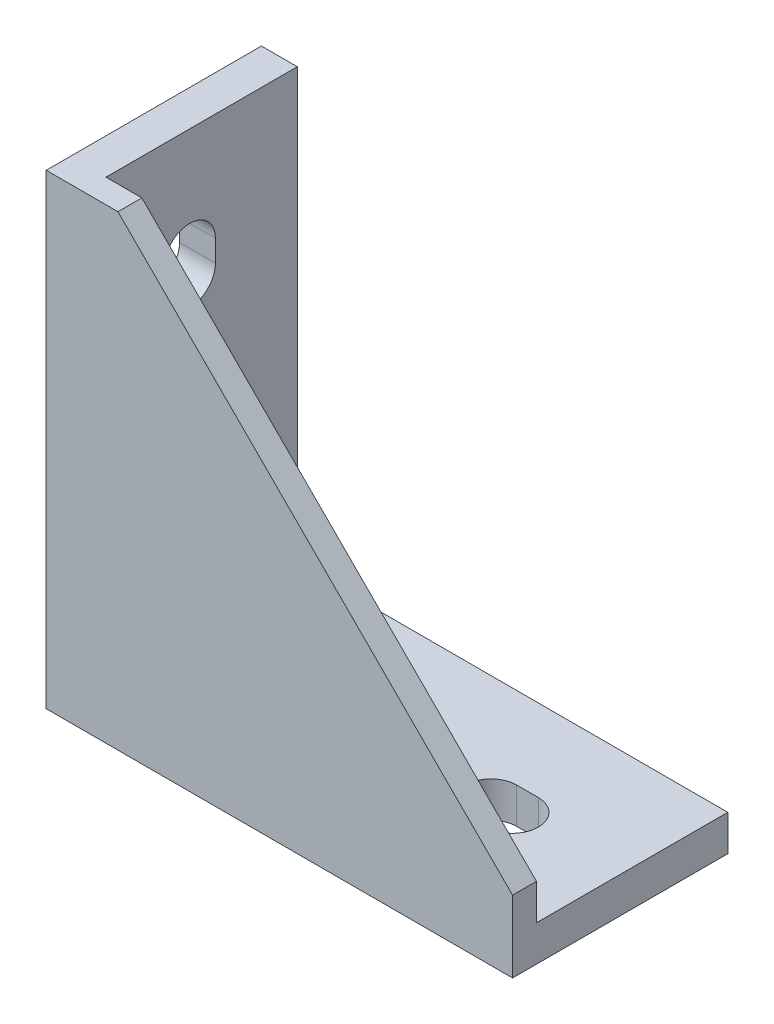
SolidWorks part; units mm, degrees
material "Алюминиевый сплав"
ref_plane "Спереди" through (0, 0, 0) normal (0, 0, 1) x (1, 0, 0)
ref_plane "Сверху" through (0, 0, 0) normal (0, 1, 0) x (1, 0, 0)
ref_plane "Справа" through (0, 0, 0) normal (1, 0, 0) x (0, 0, -1)
sketch "Эскиз1" plane through (0, 0, 0) normal (0, 0, 1) x (1, 0, 0)
  line L0 (0, 78) -> (0, 0)
  line L1 (0, 0) -> (78, 0)
  line L2 (78, 0) -> (78, 6)
  line L4 (6, 78) -> (0, 78)
  line L5 (6, 78) -> (6, 6)
  line L6 (6, 6) -> (78, 6)
  dimension "D1" = 78
  dimension "D2" = 6
extrude "Бобышка-Вытянуть1" add sketch "Эскиз1" along normal mid plane 36
sketch "Эскиз2" plane through (0, 0, 18) normal (0, 0, 1) x (1, 0, 0)
  line L1 (78, 6) -> (6, 6)
  line L2 (6, 6) -> (6, 78)
  line L3 (78, 0) -> (78, 6) construction
  line L4 (6, 78) -> (12, 78)
  line L5 (12, 78) -> (78, 12)
  line L6 (78, 12) -> (78, 6)
extrude "Бобышка-Вытянуть2" add sketch "Эскиз2" against normal blind 4
sketch "Эскиз3" plane through (0, 6, 0) normal (0, 1, 0) x (1, 0, 0)
  line L0 (18, 0) -> (31.4, 0) construction
  line L1 (18, 4.3) -> (31.4, 4.3)
  line L2 (18, -4.3) -> (31.4, -4.3)
  line L3 (0, -18) -> (0, 18) construction
  line L4 (56.4, 0) -> (60, 0) construction
  line L5 (56.4, 4.3) -> (60, 4.3)
  line L6 (56.4, -4.3) -> (60, -4.3)
  arc A0 (18, 4.3) -> (18, -4.3) centre (18, 0) ccw
  arc A1 (31.4, -4.3) -> (31.4, 4.3) centre (31.4, 0) ccw
  arc A3 (56.4, 4.3) -> (56.4, -4.3) centre (56.4, 0) ccw
  arc A4 (60, -4.3) -> (60, 4.3) centre (60, 0) ccw
  point P2 (24.7, 0)
  point P12 (58.2, 0)
  dimension "D2" = 4.3
  dimension "D3" = 18
  dimension "D4" = 3.6
  dimension "D5" = 25
  dimension "D1" = 13.4
extrude "Вырез-Вытянуть1" cut sketch "Эскиз3" against normal through all
sketch "Эскиз4" plane through (0, 0, 0) normal (0, -1, 0) x (1, 0, 0)
  line L0 (0, 18) -> (0, -18) construction
  line L1 (3, -3.75) -> (5.5, -3.75)
  line L2 (3, -3.75) -> (3, 3.75)
  line L3 (3, 3.75) -> (5.5, 3.75)
  line L4 (5.5, -3.75) -> (5.5, 3.75)
  line L5 (3, -3.75) -> (5.5, 3.75) construction
  line L6 (3, 3.75) -> (5.5, -3.75) construction
  line L7 (72.5, -3.75) -> (75, -3.75)
  line L8 (72.5, -3.75) -> (72.5, 3.75)
  line L9 (72.5, 3.75) -> (75, 3.75)
  line L10 (75, -3.75) -> (75, 3.75)
  line L11 (72.5, -3.75) -> (75, 3.75) construction
  line L12 (72.5, 3.75) -> (75, -3.75) construction
  line L13 (78, 18) -> (78, -18) construction
  point P0 (4.25, 0)
  point P5 (73.75, 0)
  dimension "D1" = 3
  dimension "D2" = 2.5
  dimension "D3" = 7.5
  dimension "D4" = 3
extrude "Бобышка-Вытянуть3" add sketch "Эскиз4" along normal blind 2.5
ref_plane "Плоскость1" through (0, 0, 0) normal (-0.7071, 0.7071, 0) x (0.7071, 0.7071, 0)
mirror "Зеркальное отражение3" about plane through (0, 0, 0) normal (-0.7071, 0.7071, 0) of "Бобышка-Вытянуть3", "Вырез-Вытянуть1"
